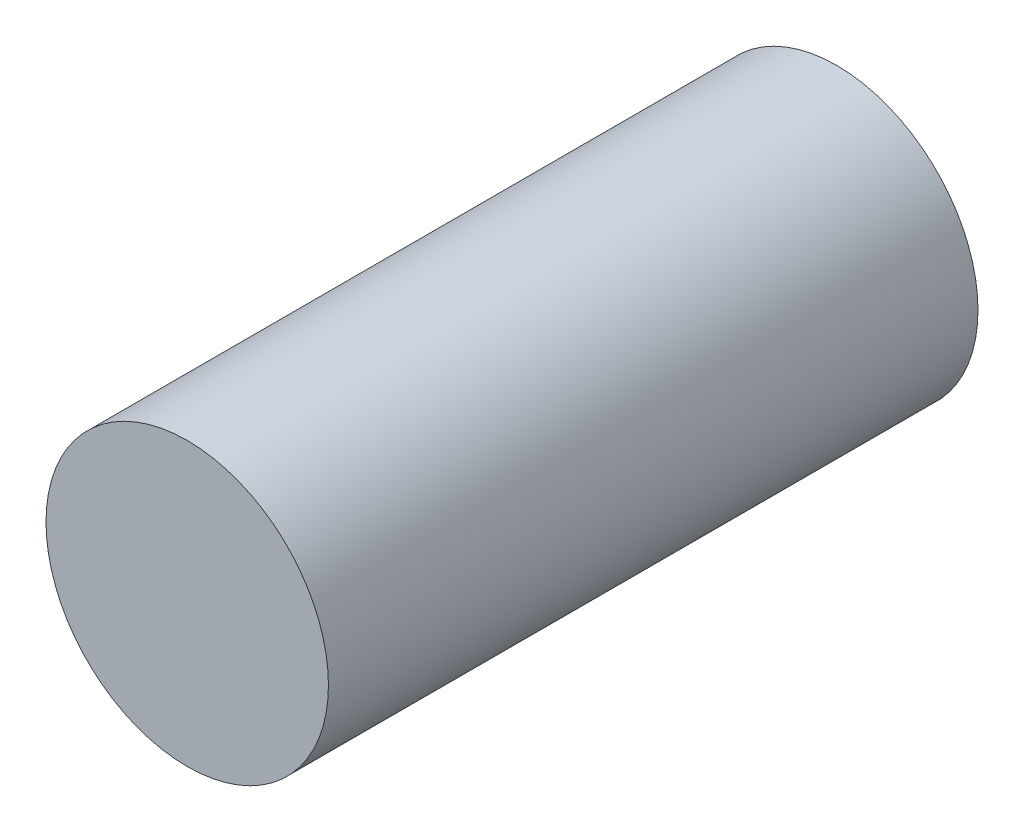
SolidWorks part; units mm, degrees
material "Stainless Steel (ferritic)"
ref_plane "Front Plane" through (0, 0, 0) normal (0, 0, 1) x (1, 0, 0)
ref_plane "Top Plane" through (0, 0, 0) normal (0, 1, 0) x (1, 0, 0)
ref_plane "Right Plane" through (0, 0, 0) normal (1, 0, 0) x (0, 0, -1)
sketch "Sketch1" plane through (0, 0, 0) normal (0, 0, 1) x (1, 0, 0)
  circle A0 centre (0, 0) radius 1.27
  dimension "D1" = 2.54
extrude "Boss-Extrude1" add sketch "Sketch1" along normal blind 5.842
